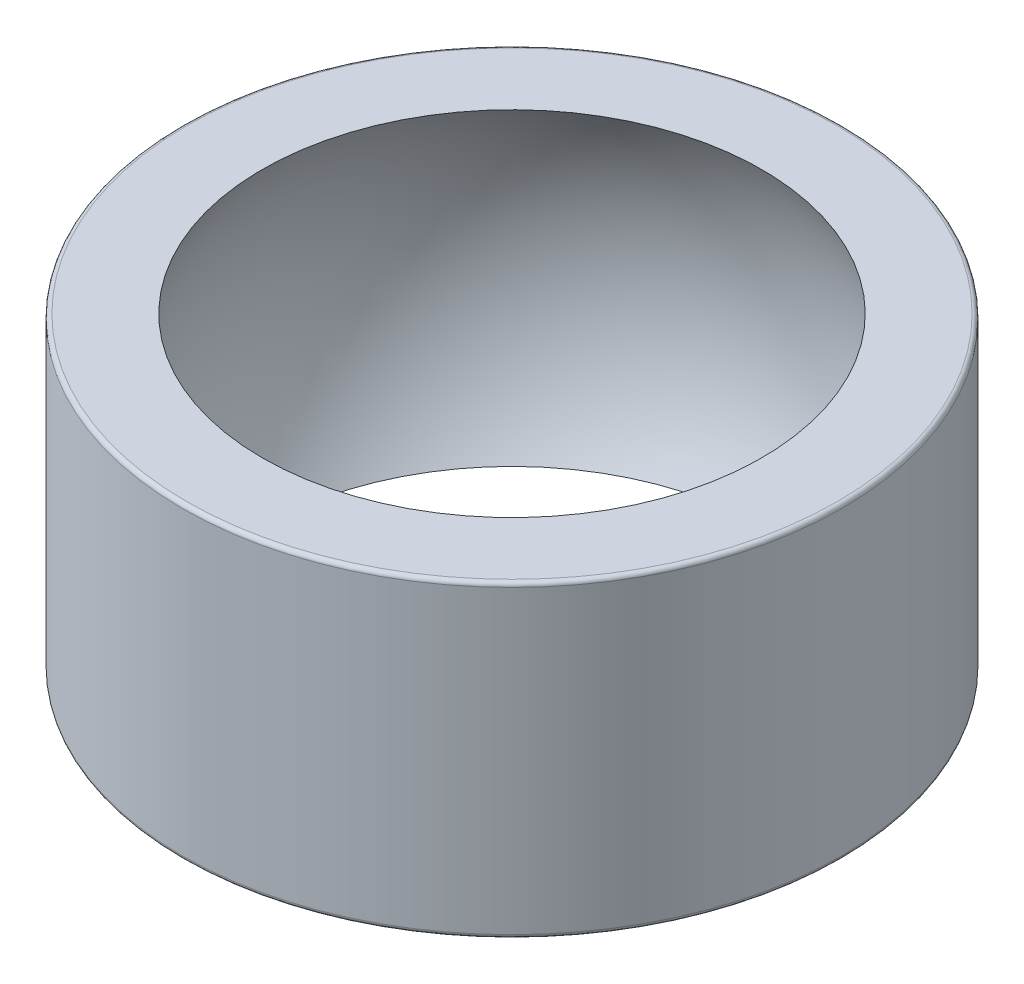
SolidWorks part; units mm, degrees
material "1.0545 (S355N)"
ref_plane "Płaszczyzna przednia" through (0, 0, 0) normal (0, 0, 1) x (1, 0, 0)
ref_plane "Płaszczyzna górna" through (0, 0, 0) normal (0, 1, 0) x (1, 0, 0)
ref_plane "Płaszczyzna prawa" through (0, 0, 0) normal (1, 0, 0) x (0, 0, -1)
sketch "Szkic1" plane through (0, 0, 0) normal (0, 1, 0) x (1, 0, 0)
  circle A0 centre (0, 0) radius 16
  dimension "d2" = 32
extrude "Dodanie-wyciągnięcie1" add sketch "Szkic1" along normal mid plane 15
sketch "Szkic3" plane through (0, 0, 0) normal (0, 0, 1) x (1, 0, 0)
  line L0 (0, -14.26) -> (0, 14.26)
  arc A0 (0, -14.26) -> (0, 14.26) centre (0, 0) ccw
  dimension "d3" = 28.52
revolve "Wycięcie-obrót1" cut sketch "Szkic3" angle 360 about L0
fillet "Zaokrąglenie1" radius 0.2 2 edges at (0, 7.5, 16) (0, -7.5, 16)
